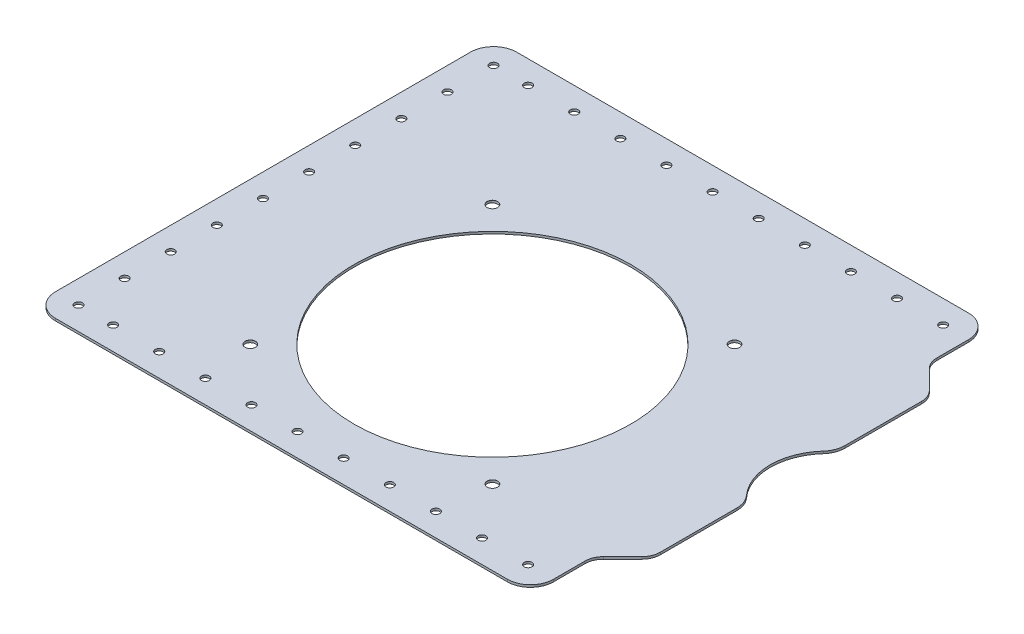
SolidWorks part; units mm, degrees
material "3003-H12"
ref_plane "Front Plane" through (0, 0, 0) normal (0, 0, 1) x (1, 0, 0)
ref_plane "Top Plane" through (0, 0, 0) normal (0, 1, 0) x (1, 0, 0)
ref_plane "Right Plane" through (0, 0, 0) normal (1, 0, 0) x (0, 0, -1)
sketch "Sketch1" plane through (0, 0, 0) normal (0, 1, 0) x (1, 0, 0)
  line L1 (-114.5, 100) -> (114.5, 100)
  line L2 (-114.5, 100) -> (-114.5, -100)
  line L3 (-114.5, -100) -> (114.5, -100)
  line L4 (114.5, 100) -> (114.5, -100)
  line L5 (-114.5, 100) -> (114.5, -100) construction
  line L6 (-114.5, -100) -> (114.5, 100) construction
  point P0 (0, 0)
  dimension "D1" = 229
  dimension "D2" = 200
extrude "Boss-Extrude1" add sketch "Sketch1" along normal blind 1
sketch "Sketch2" plane through (0, 1, 0) normal (0, 1, 0) x (1, 0, 0)
  line L0 (114.5, 60) -> (101.5, 73)
  line L1 (114.5, -100) -> (114.5, 100) construction
  line L2 (101.5, 73) -> (101.5, 100)
  line L3 (114.5, 100) -> (-114.5, 100) construction
  line L4 (101.5, 100) -> (114.5, 100)
  line L5 (114.5, 100) -> (114.5, 60)
  line L6 (-0.55, 0) -> (0.55, 0) construction
  line L7 (101.5, -100) -> (114.5, -100)
  line L8 (101.5, -73) -> (101.5, -100)
  line L9 (114.5, -60) -> (101.5, -73)
  line L10 (114.5, -100) -> (114.5, -60)
  dimension "D1" = 40
  dimension "D2" = 27
  dimension "D3" = 13
extrude "Cut-Extrude1" cut sketch "Sketch2" against normal through all
fillet "Fillet1" radius 8 4 edges at (101.5, 0.5, 73) (114.5, 0.5, 60) (114.5, 0.5, -60) (101.5, 0.5, -73)
fillet "Fillet2" radius 10 4 edges at (-114.5, 0.5, -100) (-114.5, 0.5, 100) (101.5, 0.5, 100) (101.5, 0.5, -100)
hole_wizard "M3 Clearance Hole1" positions "Sketch3" profile "Sketch4" hole size "M3" standard "ANSI Metric" end condition through all
sketch "Sketch3" plane through (0, 0, 0) normal (0, -1, 0) x (-1, 0, 0)
  line L0 (-91.5, 100) -> (104.5, 100) construction
  line L1 (114.5, 90) -> (114.5, -90) construction
  point P0 (104.5, 90)
  point P13 (104.5, 70)
  point P14 (104.5, 50)
  point P15 (104.5, 30)
  point P16 (104.5, 10)
  point P17 (104.5, -10)
  point P18 (104.5, -30)
  point P19 (104.5, -50)
  point P20 (104.5, -70)
  point P21 (104.5, -90)
  dimension "D1" = 10
  dimension "D2" = 10
  dimension "D4" = 20
  dimension "D3" = 10
sketch "Sketch4" plane through (-104.5, 0, -90) normal (1, 0, 0) x (0, 0, -1)
  line L0 (0, 0) -> (0, 1)
  line L1 (0, 1) -> (1.7, 1)
  line L2 (1.7, 1) -> (1.7, 0.025)
  line L3 (1.7, 0.025) -> (1.725, 0)
  line L5 (1.725, 0) -> (0, 0)
  line L6 (-1.7, 0.025) -> (-1.725, 0) construction
  line L11 (0, -6.35) -> (0, 107.95) construction
  dimension "Thru Hole Dia." = 3.4
  dimension "Thru Hole Depth" = 1
  dimension "Near C'Sink Dia." = 3.45
  dimension "Near C'Sink Angle" = 90
hole_wizard "M3 Clearance Hole2" positions "Sketch5" profile "Sketch6" hole size "M3" standard "ANSI Metric" end condition through all
sketch "Sketch5" plane through (0, 0, 0) normal (0, -1, 0) x (-1, 0, 0)
  line L0 (-101.5, 90) -> (-101.5, 76.3137) construction
  line L1 (-91.5, 100) -> (104.5, 100) construction
  line L2 (-0.55, 0) -> (0.55, 0) construction
  point P0 (-90.5, 90)
  point P14 (-70.5, 90)
  point P15 (-50.5, 90)
  point P16 (-30.5, 90)
  point P17 (-10.5, 90)
  point P18 (9.5, 90)
  point P19 (29.5, 90)
  point P20 (49.5, 90)
  point P21 (69.5, 90)
  point P22 (89.5, 90)
  point P25 (89.5, -90)
  point P26 (69.5, -90)
  point P27 (49.5, -90)
  point P28 (29.5, -90)
  point P29 (9.5, -90)
  point P30 (-10.5, -90)
  point P31 (-30.5, -90)
  point P32 (-50.5, -90)
  point P33 (-70.5, -90)
  point P34 (-90.5, -90)
  dimension "D1" = 11
  dimension "D2" = 10
  dimension "D4" = 20
  dimension "D3" = 10
sketch "Sketch6" plane through (90.5, 0, -90) normal (1, 0, 0) x (0, 0, -1)
  line L0 (0, 0) -> (0, 1)
  line L1 (0, 1) -> (1.7, 1)
  line L2 (1.7, 1) -> (1.7, 0.025)
  line L3 (1.7, 0.025) -> (1.725, 0)
  line L5 (1.725, 0) -> (0, 0)
  line L6 (-1.7, 0.025) -> (-1.725, 0) construction
  line L11 (0, -6.35) -> (0, 107.95) construction
  dimension "Thru Hole Dia." = 3.4
  dimension "Thru Hole Depth" = 1
  dimension "Near C'Sink Dia." = 3.45
  dimension "Near C'Sink Angle" = 90
sketch "Sketch7" plane through (0, 0, 0) normal (0, -1, 0) x (-1, 0, 0)
  line L0 (-114.5, 0) -> (-130.5, 0) construction
  line L1 (-114.5, -56.6863) -> (-114.5, 56.6863) construction
  circle A0 centre (-130.5, 0) radius 25
  dimension "D2" = 50
  dimension "D1" = 16
extrude "Cut-Extrude2" cut sketch "Sketch7" against normal blind 10
fillet "Fillet3" radius 10 2 edges at (114.5, 0.5, 19.2094) (114.5, 0.5, -19.2094)
sketch "Sketch8" plane through (0, 1, 0) normal (0, 1, 0) x (1, 0, 0)
  line L1 (-52.5, 37.5) -> (52.5, 37.5) construction
  line L2 (-52.5, 37.5) -> (-52.5, -67.5) construction
  line L3 (-52.5, -67.5) -> (52.5, -67.5) construction
  line L4 (52.5, 37.5) -> (52.5, -67.5) construction
  line L5 (-52.5, 37.5) -> (52.5, -67.5) construction
  line L6 (-52.5, -67.5) -> (52.5, 37.5) construction
  line L8 (0, 0) -> (0, -15) construction
  point P0 (0, -15)
  point P1 (52.5, -67.5)
  point P2 (-52.5, 37.5)
  point P3 (-52.5, -67.5)
  point P4 (52.5, 37.5)
  dimension "D1" = 105
  dimension "D2" = 15
hole_wizard "M4 Clearance Hole1" positions "Sketch8" profile "Sketch9" hole size "M4" standard "ANSI Metric"
sketch "Sketch9" plane through (52.5, 1, -37.5) normal (1, 0, 0) x (0, 0, 1)
  line L0 (0, 0) -> (0, 1)
  line L1 (0, 1) -> (2.25, 1)
  line L2 (2.25, 1) -> (2.25, 0.025)
  line L3 (2.25, 0.025) -> (2.275, 0)
  line L5 (2.275, 0) -> (0, 0)
  line L6 (-2.25, 0.025) -> (-2.275, 0) construction
  line L11 (0, -6.35) -> (0, 107.95) construction
  dimension "Thru Hole Dia." = 4.5
  dimension "Thru Hole Depth" = 1
  dimension "Near C'Sink Dia." = 4.55
  dimension "Near C'Sink Angle" = 90
sketch "Sketch10" plane through (0, 1, 0) normal (0, 1, 0) x (1, 0, 0)
  line L0 (-52.5, -67.5) -> (52.5, -67.5) construction
  line L1 (0, -67.5) -> (0, -15) construction
  circle A0 centre (0, -15) radius 60
  dimension "D1" = 120
  dimension "D2" = 52.5
extrude "Cut-Extrude3" cut sketch "Sketch10" against normal blind 10
